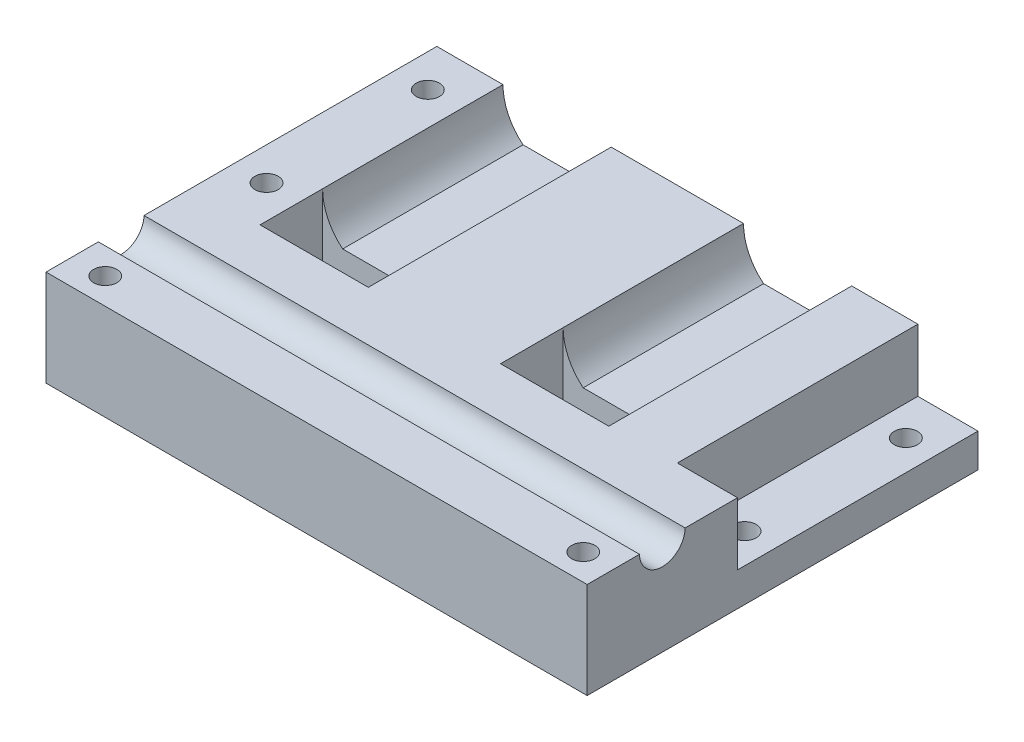
SolidWorks part; units mm, degrees
ref_plane "Front Plane" through (0, 0, 0) normal (0, 0, 1) x (1, 0, 0)
ref_plane "Top Plane" through (0, 0, 0) normal (0, 1, 0) x (1, 0, 0)
ref_plane "Right Plane" through (0, 0, 0) normal (1, 0, 0) x (0, 0, -1)
sketch "Sketch1" plane through (0, 0, 0) normal (0, 0, 1) x (1, 0, 0)
  line L0 (-50.8, 0) -> (50.8, 0)
  line L1 (50.8, 0) -> (50.8, 20.32)
  line L2 (50.8, 20.32) -> (36.83, 20.32)
  line L3 (25.4, 20.32) -> (51.7323, 20.32) construction
  line L4 (13.97, 20.32) -> (-13.97, 20.32)
  line L5 (32.5842, 11.43) -> (18.2158, 11.43)
  line L6 (0, 0) -> (0, 35.6145) construction
  line L7 (-25.4, 20.32) -> (-51.7323, 20.32) construction
  line L8 (-32.5842, 11.43) -> (-18.2158, 11.43)
  line L9 (-50.8, 20.32) -> (-36.83, 20.32)
  line L10 (-50.8, 0) -> (-50.8, 20.32)
  arc A0 (13.97, 20.32) -> (18.2158, 11.43) centre (25.4, 20.32) ccw
  arc A1 (32.5842, 11.43) -> (36.83, 20.32) centre (25.4, 20.32) ccw
  arc A2 (-32.5842, 11.43) -> (-36.83, 20.32) centre (-25.4, 20.32) cw
  arc A3 (-13.97, 20.32) -> (-18.2158, 11.43) centre (-25.4, 20.32) cw
  point P13 (43.815, 20.32)
  point P20 (0, 20.32)
  point P23 (-43.815, 20.32)
  dimension "D1" = 22.86
  dimension "D2" = 8.89
  dimension "D3" = 20.32
  dimension "D4" = 25.4
  dimension "D5" = 50.8
extrude "Boss-Extrude1" add sketch "Sketch1" along normal blind 38.1
sketch "Sketch7" plane through (0, 0, 38.1) normal (0, 0, 1) x (1, 0, 0)
  line L1 (-50.8, 20.32) -> (50.8, 20.32)
  line L2 (-50.8, 20.32) -> (-50.8, 0)
  line L3 (-50.8, 0) -> (50.8, 0)
  line L4 (50.8, 20.32) -> (50.8, 0)
extrude "Boss-Extrude2" add sketch "Sketch7" along normal blind 44.45
sketch "Sketch20" plane through (50.8, 0, 0) normal (1, 0, 0) x (0, 0, -1)
  line L0 (-82.55, 0) -> (-82.55, 20.32) construction
  line L1 (0, 0) -> (-82.55, 0)
  line L2 (0, 0) -> (0, 7.112)
  line L3 (0, 7.112) -> (-50.8, 7.112)
  line L4 (-82.55, 0) -> (-82.55, 3.8743)
  line L5 (-82.55, 20.32) -> (0, 20.32) construction
  line L6 (-82.55, 0) -> (-50.8, 0)
  line L7 (-82.55, 0) -> (-82.55, 20.32)
  line L8 (-82.55, 20.32) -> (-50.8, 20.32)
  line L9 (-50.8, 7.112) -> (-50.8, 20.32)
  dimension "D1" = 50.8
  dimension "D2" = 7.112
extrude "Boss-Extrude8" add sketch "Sketch20" along normal blind 12.7
sketch "Sketch21" [suppressed] plane through (-50.8, 0, 0) normal (-1, 0, 0) x (0, 0, 1)
  line L0 (82.55, 20.32) -> (82.55, 0) construction
  line L1 (0, 0) -> (82.55, 0)
  line L2 (0, 0) -> (0, 7.112)
  line L3 (0, 7.112) -> (50.8, 7.112)
  line L4 (82.55, 0) -> (82.55, 7.1535)
  line L5 (82.55, 20.32) -> (0, 20.32) construction
  line L6 (82.55, 0) -> (68.4145, 0)
  line L7 (82.55, 0) -> (82.55, 20.32)
  line L8 (82.55, 20.32) -> (50.8, 20.32)
  line L9 (50.8, 7.112) -> (50.8, 20.32)
  line L10 (0, 20.32) -> (0, 0) construction
  point P15 (50.8, 13.716)
  dimension "D1" = 7.112
  dimension "D2" = 50.8
extrude "Boss-Extrude9" [suppressed] add sketch "Sketch21" along normal blind 12.7
sketch "Sketch8" plane through (0, 20.32, 0) normal (0, 1, 0) x (1, 0, 0)
  line L0 (0, 0) -> (0, -81.5203) construction
  line L1 (-13.97, -38.1) -> (-13.97, 0) construction
  line L2 (-36.83, -38.1) -> (-13.97, -38.1)
  line L3 (-36.83, -38.1) -> (-36.83, -51.308)
  line L4 (-36.83, -51.308) -> (-13.97, -51.308)
  line L5 (-13.97, -38.1) -> (-13.97, -51.308)
  line L6 (13.97, -38.1) -> (13.97, -51.308)
  line L7 (36.83, -51.308) -> (13.97, -51.308)
  line L8 (36.83, -38.1) -> (36.83, -51.308)
  line L9 (36.83, -38.1) -> (13.97, -38.1)
  line L10 (63.5, -50.8) -> (50.8, -50.8) construction
  line L12 (63.5, -50.8) -> (50.8, -50.8) construction
  line L13 (50.8, 0) -> (36.83, 0) construction
  line L14 (50.8, 0) -> (36.83, 0) construction
  line L15 (-36.83, 0) -> (-50.8, 0) construction
  line L16 (-36.83, 0) -> (-50.8, 0) construction
  point P19 (43.815, 0)
  point P20 (57.15, -50.8)
  point P23 (-43.815, 0)
  dimension "D1" = 13.208
extrude "Cut-Extrude1" cut sketch "Sketch8" against normal up to surface (20.32 mm away) up to face at (6.35, 0, 41.275)
hole_wizard "#10 (0.1935) Diameter Hole1" positions "Sketch4" profile "Sketch5" hole size "#10" standard "ANSI Inch"
sketch "Sketch4" plane through (0, 20.32, 0) normal (0, 1, 0) x (1, 0, 0)
  point P0 (-43.815, -8.89)
  dimension "D2" = 8.89
sketch "Sketch5" plane through (-43.815, 20.32, 8.89) normal (1, 0, 0) x (0, 0, 1)
  line L0 (0, 0) -> (0, 25.4)
  line L1 (0, 25.4) -> (2.4574, 23.9234)
  line L2 (2.4574, 23.9234) -> (2.4574, 0)
  line L5 (2.4574, 0) -> (0, 0)
  line L10 (0, 25.4) -> (-2.4575, 23.9234) construction
  line L11 (0, -6.35) -> (0, 107.95) construction
  dimension "Hole Dia." = 4.9149
  dimension "Hole Depth" = 25.4
  dimension "Drill Angle" = 118
sketch "Sketch9" plane through (-50.8, 0, 0) normal (-1, 0, 0) x (0, 0, 1)
  line L1 (82.55, 20.32) -> (0, 20.32) construction
  line L2 (0, 20.32) -> (0, 0) construction
  line L3 (82.55, 20.32) -> (71.4993, 20.32) construction
  line L4 (38.1, 20.32) -> (51.308, 20.32) construction
  line L5 (38.1, 20.32) -> (51.308, 20.32) construction
  circle A0 centre (66.675, 20.447) radius 4.826
  point P11 (44.704, 20.32)
  point P12 (77.0247, 20.32)
  dimension "D2" = 9.652
  dimension "D1" = 66.675
  dimension "D3" = 0.127
extrude "Cut-Extrude2" cut sketch "Sketch9" along direction (-1, 0, 0) on the side against the normal up to surface (114.3 mm away) contours A0
pattern_linear "LPattern1" count 3 spacing 34.0673 along (0, 0, 1) count 2 spacing 100.965 along (1, 0, 0) of "#10 (0.1935) Diameter Hole1"
